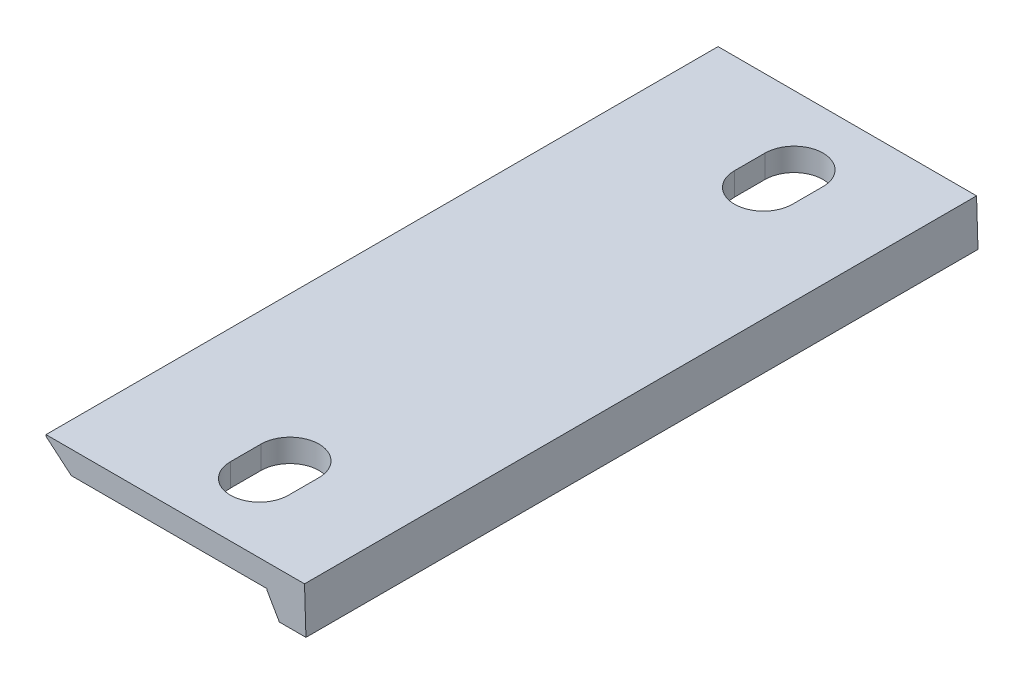
SolidWorks part; units mm, degrees
ref_plane "Спереди" through (0, 0, 0) normal (0, 0, 1) x (1, 0, 0)
ref_plane "Сверху" through (0, 0, 0) normal (0, 1, 0) x (1, 0, 0)
ref_plane "Справа" through (0, 0, 0) normal (1, 0, 0) x (0, 0, -1)
sketch "Эскиз1" plane through (0, 0, 0) normal (0, 0, 1) x (1, 0, 0)
  line L0 (169.2529, 0) -> (0, 0)
  line L1 (16.565, -15) -> (144.7482, -15)
  line L2 (144.7482, -15) -> (144.7482, -16)
  line L3 (170.1935, -29.9062) -> (152.777, -29.9062)
  line L9 (170.1935, -29.9062) -> (169.2529, 0)
  line L11 (0, 0) -> (0, -1)
  line L12 (0, -1) -> (16.565, -15)
  line L13 (144.7482, -16) -> (152.777, -29.9062)
  dimension "D1" = 1
  dimension "D2" = 1
  dimension "D3" = 30
extrude "Бобышка-Вытянуть1" add sketch "Эскиз1" against normal blind 440
sketch "Эскиз4" plane through (0, 0, 0) normal (0, 1, 0) x (1, 0, 0)
  line L0 (75.7482, 65) -> (75.7482, 45)
  line L1 (113.7482, 45) -> (113.7482, 65)
  line L2 (75.7482, 395) -> (75.7482, 375)
  line L3 (113.7482, 375) -> (113.7482, 395)
  arc A0 (75.7482, 45) -> (113.7482, 45) centre (94.7482, 45) ccw
  arc A1 (113.7482, 65) -> (75.7482, 65) centre (94.7482, 65) ccw
  arc A2 (75.7482, 375) -> (113.7482, 375) centre (94.7482, 375) ccw
  arc A3 (113.7482, 395) -> (75.7482, 395) centre (94.7482, 395) ccw
extrude "Вырез-Вытянуть1" cut sketch "Эскиз4" against normal through all
